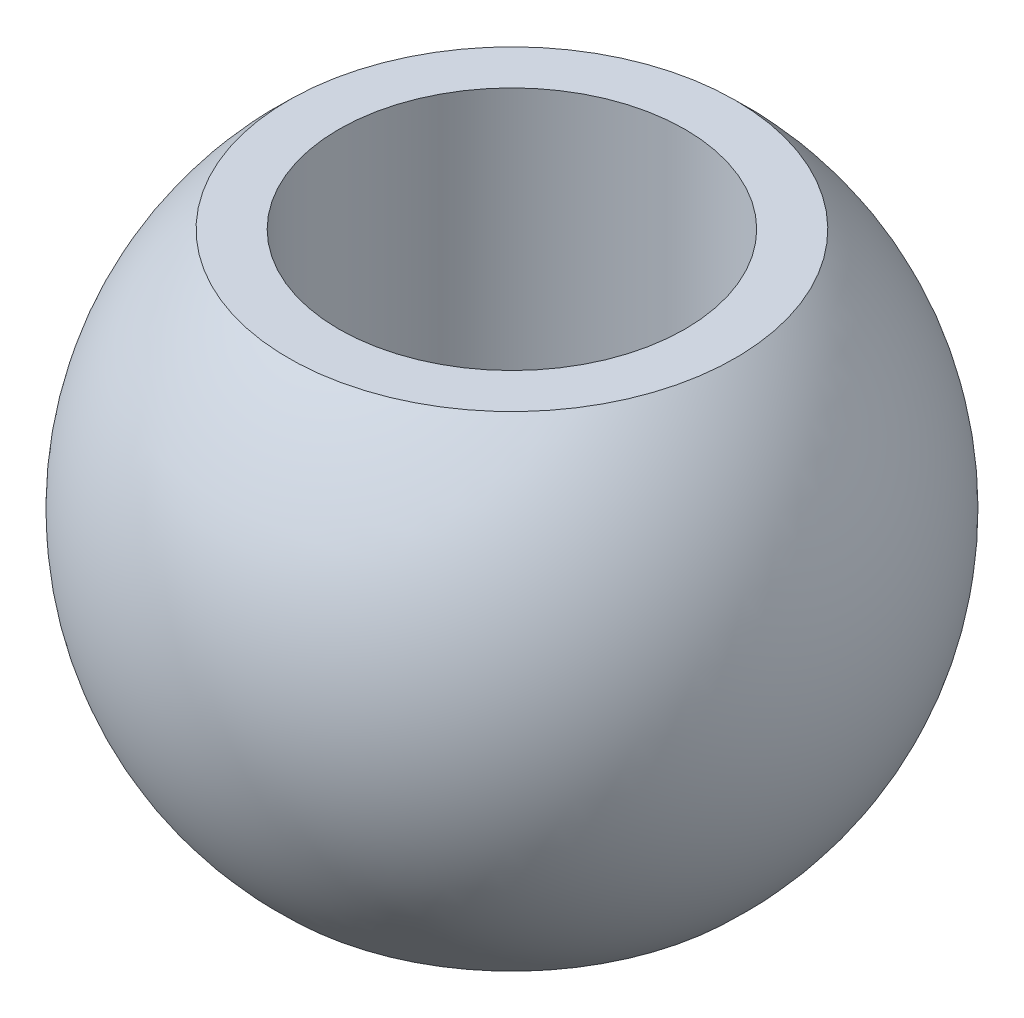
SolidWorks part; units mm, degrees
material "1.0545 (S355N)"
ref_plane "Płaszczyzna przednia" through (0, 0, 0) normal (0, 0, 1) x (1, 0, 0)
ref_plane "Płaszczyzna górna" through (0, 0, 0) normal (0, 1, 0) x (1, 0, 0)
ref_plane "Płaszczyzna prawa" through (0, 0, 0) normal (1, 0, 0) x (0, 0, -1)
sketch "Szkic1" plane through (0, 0, 0) normal (0, 0, 1) x (1, 0, 0)
  line L0 (0, -11.1) -> (0, 11.1) construction
  line L1 (5, -7) -> (5, 7)
  line L2 (5, 7) -> (6.4522, 7)
  line L3 (5, -7) -> (6.4522, -7)
  arc A0 (6.4522, -7) -> (6.4522, 7) centre (0, 0) ccw
  point P6 (5, 0)
  dimension "d3" = 19.04
  dimension "d1" = 5
  dimension "b1" = 14
revolve "Obrót1" add sketch "Szkic1" angle 360 about L0
